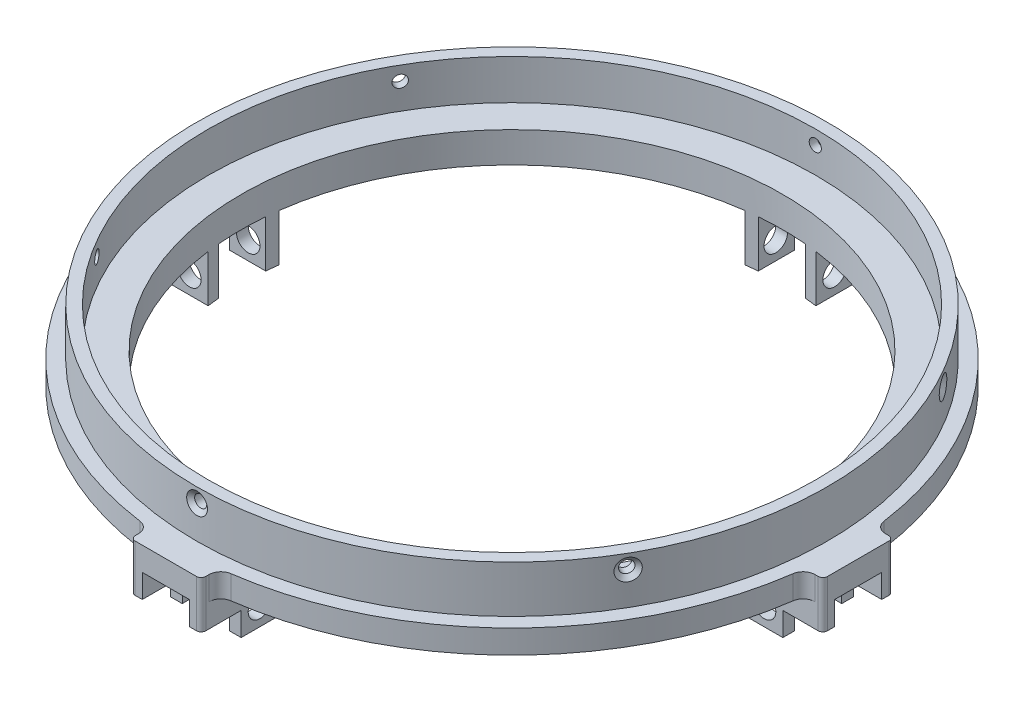
SolidWorks part; units mm, degrees
material "ASTM A36 Steel"
ref_plane "Front" through (0, 0, 0) normal (0, 0, 1) x (1, 0, 0)
ref_plane "Top" through (0, 0, 0) normal (0, 1, 0) x (1, 0, 0)
ref_plane "Right" through (0, 0, 0) normal (1, 0, 0) x (0, 0, -1)
sketch "Sketch1" plane through (0, 0, 0) normal (0, 1, 0) x (1, 0, 0)
  line L1 (-152.4, 152.4) -> (152.4, 152.4)
  line L2 (-152.4, 152.4) -> (-152.4, -152.4)
  line L3 (-152.4, -152.4) -> (152.4, -152.4)
  line L4 (152.4, 152.4) -> (152.4, -152.4)
  line L5 (-152.4, 152.4) -> (152.4, -152.4) construction
  line L6 (-152.4, -152.4) -> (152.4, 152.4) construction
  point P0 (0, 0)
  dimension "D1" = 304.8
  dimension "D2" = 304.8
extrude "Boss-Extrude1" add sketch "Sketch1" along normal blind 19.05
sketch "Sketch2" plane through (0, 19.05, 0) normal (0, 1, 0) x (1, 0, 0)
  circle A0 centre (0, 0) radius 81.915
  dimension "D1" = 163.83
extrude "Cut-Extrude1" cut sketch "Sketch2" against normal blind 10.795
sketch "Sketch3" plane through (0, 8.255, 0) normal (0, 1, 0) x (1, 0, 0)
  circle A0 centre (0, 0) radius 73.025
  dimension "D1" = 146.05
extrude "Cut-Extrude2" cut sketch "Sketch3" against normal up to next
sketch "Sketch4" plane through (0, 19.05, 0) normal (0, 1, 0) x (1, 0, 0)
  circle A0 centre (0, 0) radius 85.09
  dimension "D1" = 170.18
extrude "Cut-Extrude4" cut sketch "Sketch4" against normal blind 12.7 flip side to cut
hole_wizard "CSK for #4 Flat Head Machine Screw (100)1" positions "3DSketch6" profile "Sketch10" countersink size "#4" standard "ANSI Inch"
sketch3d "3DSketch6"
  point P0 (0.1296, 15.24, 85.0899)
  dimension "D1" = 3.81
sketch "Sketch10" plane through (0.1296, 15.24, 85.0899) normal (0, 1, 0) x (1, 0, -0.0015)
  line L0 (0, 0) -> (0, 197.0349)
  line L1 (0, 197.0349) -> (1.6319, 197.0349)
  line L2 (1.6319, 197.0349) -> (1.6319, 1.0284)
  line L3 (1.6319, 1.0284) -> (2.8575, 0)
  line L5 (2.8575, 0) -> (0, 0)
  line L6 (-1.6319, 1.0284) -> (-2.8575, 0) construction
  line L11 (0, -6.35) -> (0, 107.95) construction
  dimension "Thru Hole Dia." = 3.2639
  dimension "Thru Hole Depth" = 197.0349
  dimension "Near C'Sink Dia." = 5.715
  dimension "Near C'Sink Angle" = 100
pattern_circular "CirPattern1" count 6 over 360 about axis through (0, 19.05, 0) along (0, 1, 0) of "CSK for #4 Flat Head Machine Screw (100)1"
sketch "Sketch11" plane through (0, 6.35, 0) normal (0, 1, 0) x (1, 0, 0)
  line L0 (-91.1949, 9.525) -> (-92.075, 9.525)
  line L1 (0, 0) -> (0, 88.9) construction
  line L2 (-93.345, 8.255) -> (-93.345, -8.255)
  line L3 (-92.075, -9.525) -> (-91.1949, -9.525)
  line L4 (9.525, 91.1949) -> (9.525, 92.075)
  line L5 (8.255, 93.345) -> (-8.255, 93.345)
  line L6 (-9.525, 92.075) -> (-9.525, 91.1949)
  line L7 (0, 0) -> (88.9, 0) construction
  line L8 (88.9, 0) -> (93.345, 0) construction
  line L9 (-9.525, -91.1949) -> (-9.525, -92.075)
  line L10 (-8.255, -93.345) -> (8.255, -93.345)
  line L11 (9.525, -92.075) -> (9.525, -91.1949)
  line L12 (0, 0) -> (0, -88.9) construction
  line L13 (0, -88.9) -> (0, -93.345) construction
  line L14 (91.1949, -9.525) -> (92.075, -9.525)
  line L15 (93.345, -8.255) -> (93.345, 8.255)
  line L16 (0, 88.9) -> (0, 93.345) construction
  line L17 (92.075, 9.525) -> (91.1949, 9.525)
  line L18 (0, 0) -> (-88.9, 0) construction
  line L19 (-88.9, 0) -> (-93.345, 0) construction
  circle A0 centre (0, 0) radius 85.09 construction
  arc A1 (-91.1949, 9.525) -> (-88.0503, 12.2621) centre (-91.1949, 12.7) ccw
  arc A2 (-92.075, 9.525) -> (-93.345, 8.255) centre (-92.075, 8.255) ccw
  arc A3 (-93.345, -8.255) -> (-92.075, -9.525) centre (-92.075, -8.255) ccw
  arc A4 (-91.1949, -9.525) -> (-88.0503, -12.2621) centre (-91.1949, -12.7) cw
  arc A5 (9.525, 91.1949) -> (12.2621, 88.0503) centre (12.7, 91.1949) ccw
  arc A6 (8.255, -93.345) -> (9.525, -92.075) centre (8.255, -92.075) ccw
  arc A7 (9.525, 92.075) -> (8.255, 93.345) centre (8.255, 92.075) ccw
  arc A8 (-8.255, 93.345) -> (-9.525, 92.075) centre (-8.255, 92.075) ccw
  arc A9 (-9.525, 91.1949) -> (-12.2621, 88.0503) centre (-12.7, 91.1949) cw
  circle A10 centre (0, 0) radius 73.025 construction
  arc A11 (9.525, -91.1949) -> (12.2621, -88.0503) centre (12.7, -91.1949) cw
  arc A12 (-9.525, -91.1949) -> (-12.2621, -88.0503) centre (-12.7, -91.1949) ccw
  arc A13 (-9.525, -92.075) -> (-8.255, -93.345) centre (-8.255, -92.075) ccw
  arc A14 (91.1949, -9.525) -> (88.0503, -12.2621) centre (91.1949, -12.7) ccw
  arc A15 (92.075, -9.525) -> (93.345, -8.255) centre (92.075, -8.255) ccw
  arc A16 (93.345, 8.255) -> (92.075, 9.525) centre (92.075, 8.255) ccw
  circle A17 centre (0, 0) radius 88.9
  arc A18 (91.1949, 9.525) -> (88.0503, 12.2621) centre (91.1949, 12.7) cw
  circle A22 centre (0, 0) radius 79.375 construction
  circle A23 centre (0, 0) radius 98.425 construction
  point P1 (0, 73.025)
  point P50 (0, 0)
  point P69 (0, 0)
  point P72 (0, 0)
  dimension "D1" = 3.175
  dimension "D4" = 1.27
  dimension "D7" = 177.8
  dimension "D8" = 4
  dimension "D5" = 158.75
  dimension "D9" = 19.05
  dimension "D2" = 0.8801
  dimension "D3" = 20.32
  dimension "D6" = 4
extrude "Cut-Extrude7" cut sketch "Sketch11" against normal blind 19.05
sketch "Sketch16" plane through (0, 0, 0) normal (0, 1, 0) x (1, 0, 0)
  line L1 (152.4, -152.4) -> (-152.4, -152.4) construction
  line L4 (-152.4, -152.4) -> (-152.4, 152.4) construction
  point P0 (0, 0)
  dimension "D1" = 304.8
  dimension "D2" = 304.8
  dimension "D3" = 152.4
  dimension "D4" = 152.4
sketch "Sketch18" plane through (0, 0, 0) normal (0, -1, 0) x (1, 0, 0)
  line L0 (0, 93.345) -> (0, 0) construction
  line L1 (-8.255, 93.345) -> (8.255, 93.345) construction
  line L2 (6.35, 72.7484) -> (-6.35, 72.7484) construction
  line L3 (6.35, 72.7484) -> (6.35, 93.345)
  line L4 (6.35, 93.345) -> (-6.35, 93.345) construction
  line L5 (-6.35, 72.7484) -> (-6.35, 93.345)
  line L6 (6.35, 72.7484) -> (-6.35, 93.345) construction
  line L7 (6.35, 93.345) -> (-6.35, 72.7484) construction
  line L8 (-9.525, 92.075) -> (-9.525, 72.4011)
  line L9 (-6.35, 93.345) -> (-8.255, 93.345)
  line L10 (9.525, 92.075) -> (9.525, 72.4011)
  line L11 (6.35, 93.345) -> (8.255, 93.345)
  line L12 (72.7484, -6.35) -> (93.345, -6.35)
  line L13 (72.7484, 6.35) -> (93.345, 6.35)
  line L14 (92.075, 9.525) -> (72.4011, 9.525)
  line L15 (93.345, 6.35) -> (93.345, 8.255)
  line L16 (92.075, -9.525) -> (72.4011, -9.525)
  line L17 (93.345, -6.35) -> (93.345, -8.255)
  line L18 (93.345, 0) -> (0, 0) construction
  line L19 (72.7484, -6.35) -> (72.7484, 6.35) construction
  line L20 (93.345, -6.35) -> (93.345, 6.35) construction
  line L21 (72.7484, -6.35) -> (93.345, 6.35) construction
  line L22 (93.345, -6.35) -> (72.7484, 6.35) construction
  line L23 (-6.35, -72.7484) -> (-6.35, -93.345)
  line L24 (6.35, -72.7484) -> (6.35, -93.345)
  line L25 (9.525, -92.075) -> (9.525, -72.4011)
  line L26 (6.35, -93.345) -> (8.255, -93.345)
  line L27 (-9.525, -92.075) -> (-9.525, -72.4011)
  line L28 (-6.35, -93.345) -> (-8.255, -93.345)
  line L29 (0, -93.345) -> (0, 0) construction
  line L30 (-6.35, -72.7484) -> (6.35, -72.7484) construction
  line L31 (-6.35, -93.345) -> (6.35, -93.345) construction
  line L32 (-6.35, -72.7484) -> (6.35, -93.345) construction
  line L33 (-6.35, -93.345) -> (6.35, -72.7484) construction
  line L34 (-72.7484, 6.35) -> (-93.345, 6.35)
  line L35 (-72.7484, -6.35) -> (-93.345, -6.35)
  line L36 (-92.075, -9.525) -> (-72.4011, -9.525)
  line L37 (-93.345, -6.35) -> (-93.345, -8.255)
  line L38 (-92.075, 9.525) -> (-72.4011, 9.525)
  line L39 (-93.345, 6.35) -> (-93.345, 8.255)
  line L40 (-93.345, 0) -> (0, 0) construction
  line L41 (-72.7484, 6.35) -> (-72.7484, -6.35) construction
  line L42 (-93.345, 6.35) -> (-93.345, -6.35) construction
  line L43 (-72.7484, 6.35) -> (-93.345, -6.35) construction
  line L44 (-93.345, 6.35) -> (-72.7484, -6.35) construction
  arc A0 (-6.35, 72.7484) -> (-9.525, 72.4011) centre (0, 0) ccw
  circle A1 centre (0, 0) radius 73.025 construction
  arc A2 (9.525, 72.4011) -> (6.35, 72.7484) centre (0, 0) ccw
  arc A3 (-9.525, 92.075) -> (-8.255, 93.345) centre (-8.255, 92.075) cw
  arc A4 (9.525, 92.075) -> (8.255, 93.345) centre (8.255, 92.075) ccw
  arc A5 (72.7484, 6.35) -> (72.4011, 9.525) centre (0, 0) ccw
  arc A6 (72.4011, -9.525) -> (72.7484, -6.35) centre (0, 0) ccw
  arc A7 (92.075, 9.525) -> (93.345, 8.255) centre (92.075, 8.255) cw
  arc A8 (92.075, -9.525) -> (93.345, -8.255) centre (92.075, -8.255) ccw
  arc A9 (6.35, -72.7484) -> (9.525, -72.4011) centre (0, 0) ccw
  arc A10 (-9.525, -72.4011) -> (-6.35, -72.7484) centre (0, 0) ccw
  arc A11 (9.525, -92.075) -> (8.255, -93.345) centre (8.255, -92.075) cw
  arc A12 (-9.525, -92.075) -> (-8.255, -93.345) centre (-8.255, -92.075) ccw
  arc A13 (-72.7484, -6.35) -> (-72.4011, -9.525) centre (0, 0) ccw
  arc A14 (-72.4011, 9.525) -> (-72.7484, 6.35) centre (0, 0) ccw
  arc A15 (-92.075, -9.525) -> (-93.345, -8.255) centre (-92.075, -8.255) cw
  arc A16 (-92.075, 9.525) -> (-93.345, 8.255) centre (-92.075, 8.255) ccw
  point P3 (0, 83.0467)
  point P25 (83.0467, 0)
  point P39 (0, -83.0467)
  point P53 (-83.0467, 0)
  point P66 (0, 0)
  dimension "D2" = 4
  dimension "D3" = 1.27
  dimension "D1" = 12.7
extrude "Boss-Extrude2" add sketch "Sketch18" along normal blind 12.7
sketch "Sketch19" plane through (9.525, 0, 0) normal (1, 0, 0) x (0, 0, -1)
  line L0 (-96.1332, -6.35) -> (-82.5611, -6.35)
  line L1 (-72.4011, 0) -> (-91.1949, 0) construction
  line L2 (-82.5611, -7.62) -> (-82.5611, -12.7)
  line L3 (-82.5611, -12.7) -> (-70.8041, -12.7)
  line L4 (-72.4011, -12.7) -> (-92.075, -12.7) construction
  line L5 (-82.5611, -7.62) -> (-82.5611, -6.35)
  line L7 (-70.8041, -12.7) -> (-70.8041, -20.3968)
  line L8 (-70.8041, -20.3968) -> (-96.1332, -20.3968)
  line L9 (-96.1332, -20.3968) -> (-96.1332, -6.35)
  line L10 (-72.4011, -12.7) -> (-72.4011, 0) construction
  arc A0 (-82.5611, -7.62) -> (-72.4011, -7.62) centre (-77.4811, -7.62) ccw construction
  dimension "D2" = 10.16
  dimension "D1" = 6.35
extrude "Cut-Extrude12" cut sketch "Sketch19" against normal blind 19.05
pattern_circular "CirPattern6" count 4 over 360 of "Cut-Extrude12"
sketch "Sketch20" plane through (9.525, 0, 0) normal (1, 0, 0) x (0, 0, -1)
  line L0 (-72.4011, -12.7) -> (-72.4011, 0) construction
  line L1 (-72.4011, -12.7) -> (-82.5611, -12.7) construction
  circle A0 centre (-77.4811, -7.62) radius 5.08 construction
  circle A1 centre (-77.4811, -7.62) radius 3.175
  dimension "D1" = 10.16
  dimension "D2" = 6.35
extrude "Cut-Extrude13" cut sketch "Sketch20" against normal blind 19.05
pattern_circular "CirPattern7" count 4 over 360 about axis through (0, 19.05, 0) along (0, 1, 0) of "Cut-Extrude13"
